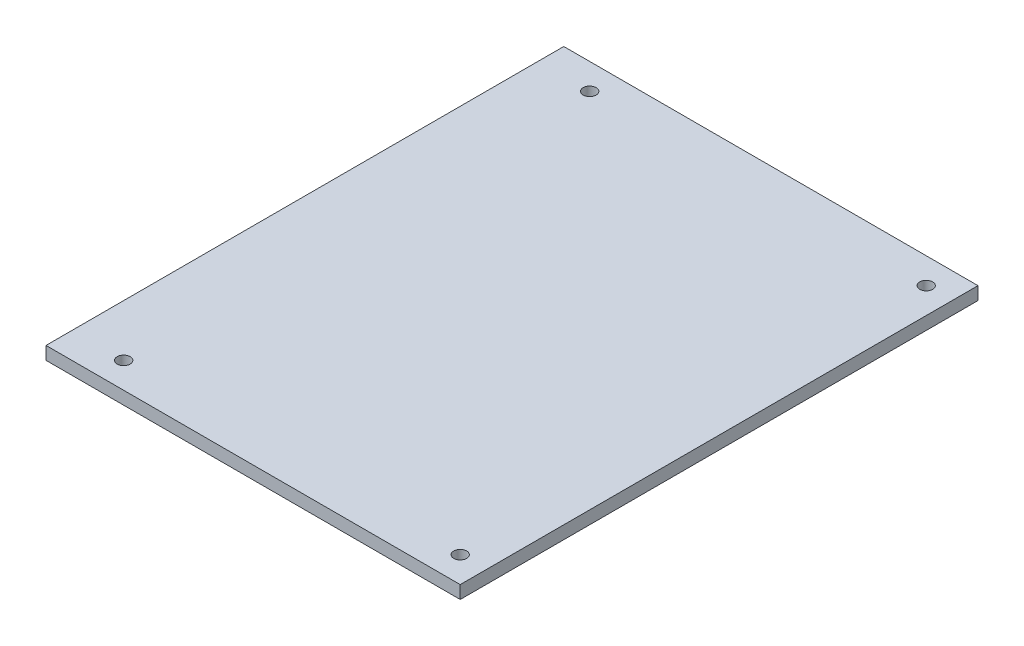
SolidWorks part; units mm, degrees
ref_plane "Front Plane" through (0, 0, 0) normal (0, 0, 1) x (1, 0, 0)
ref_plane "Top Plane" through (0, 0, 0) normal (0, 1, 0) x (1, 0, 0)
ref_plane "Right Plane" through (0, 0, 0) normal (1, 0, 0) x (0, 0, -1)
sketch "Sketch1" plane through (0, 0, 0) normal (0, 1, 0) x (1, 0, 0)
  line L1 (0, 0) -> (203.2, 0)
  line L2 (0, 0) -> (0, 254)
  line L3 (0, 254) -> (203.2, 254)
  line L4 (203.2, 0) -> (203.2, 254)
  dimension "D1" = 203.2
  dimension "D2" = 254
extrude "Boss-Extrude1" add sketch "Sketch1" along normal blind 6.35
sketch "Sketch2" plane through (0, 6.35, 0) normal (0, 1, 0) x (1, 0, 0)
  line L0 (203.2, 0) -> (203.2, 254) construction
  line L1 (203.2, 254) -> (0, 254) construction
  line L2 (0, 254) -> (0, 0) construction
  line L3 (0, 0) -> (203.2, 0) construction
  circle A0 centre (25.4, 241.3) radius 3.175
  circle A1 centre (25.4, 12.7) radius 3.175
  circle A2 centre (190.5, 12.7) radius 3.175
  circle A3 centre (190.5, 241.3) radius 3.175
  dimension "D1" = 6.35
  dimension "D2" = 6.35
  dimension "D3" = 6.35
  dimension "D4" = 6.35
  dimension "D5" = 12.7
  dimension "D6" = 12.7
  dimension "D7" = 12.7
  dimension "D8" = 25.4
  dimension "D9" = 12.7
  dimension "D10" = 12.7
  dimension "D11" = 12.7
  dimension "D12" = 25.4
extrude "Cut-Extrude1" cut sketch "Sketch2" against normal blind 25.4
